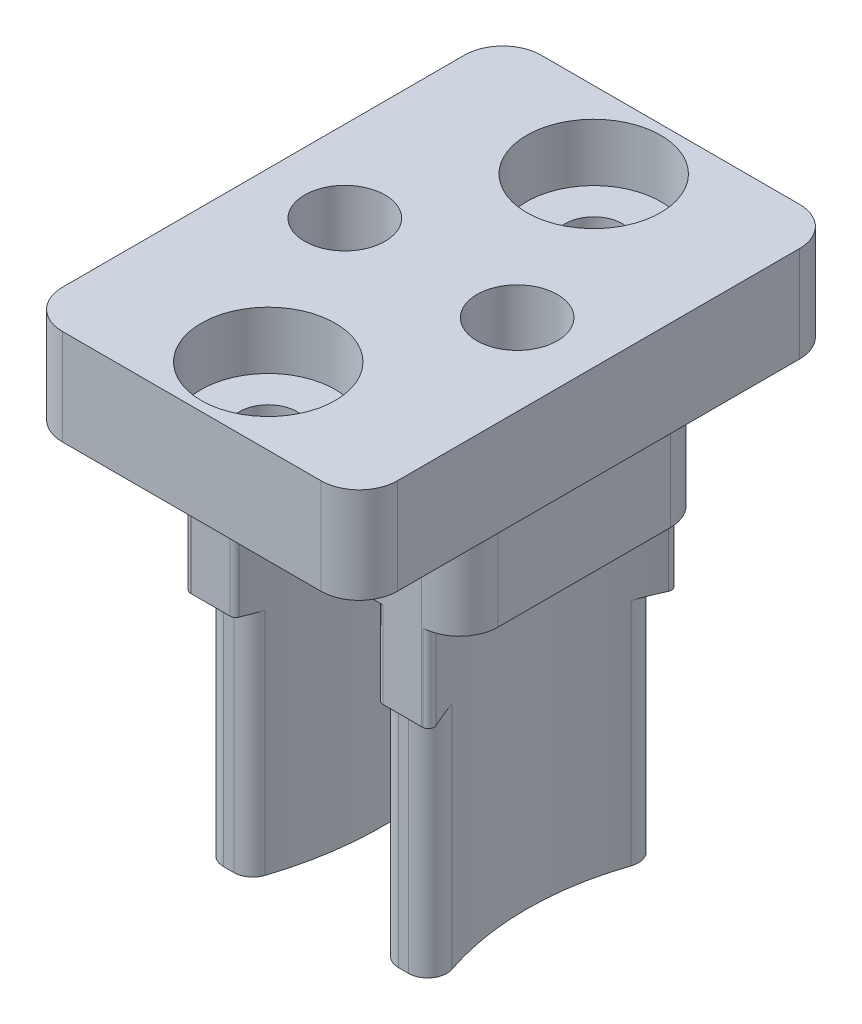
SolidWorks part; units mm, degrees
ref_plane "Front Plane" through (0, 0, 0) normal (0, 0, 1) x (1, 0, 0)
ref_plane "Top Plane" through (0, 0, 0) normal (0, 1, 0) x (1, 0, 0)
ref_plane "Right Plane" through (0, 0, 0) normal (1, 0, 0) x (0, 0, -1)
sketch "Sketch1" plane through (0, 0, 0) normal (0, 1, 0) x (1, 0, 0)
  line L1 (0, 0) -> (123.5, 0)
  line L2 (0, 0) -> (0, -81.5)
  line L3 (0, -81.5) -> (123.5, -81.5)
  line L4 (123.5, 0) -> (123.5, -81.5)
  dimension "D1" = 123.5
  dimension "D2" = 81.5
extrude "Boss-Extrude1" add sketch "Sketch1" along normal blind 8
chamfer "Chamfer1" distance 10 angle 45 2 edges at (123.5, 4, 81.5) (123.5, 4, 0)
sketch "Sketch2" plane through (0, 0, 0) normal (0, -1, 0) x (1, 0, 0)
  line L0 (0, 0) -> (0, 81.5) construction
  line L1 (-3.25, -3.25) -> (126.75, -3.25)
  line L2 (-3.25, -3.25) -> (-3.25, 84.75)
  line L3 (-3.25, 84.75) -> (126.75, 84.75)
  line L4 (126.75, -3.25) -> (126.75, 84.75)
  line L5 (113.5, 0) -> (0, 0) construction
  dimension "D1" = 88
  dimension "D2" = 130
  dimension "D3" = 3.25
  dimension "D4" = 3.25
extrude "Boss-Extrude2" add sketch "Sketch2" along normal blind 9
fillet "Fillet1" radius 2 10 edges at (113.5, 4, 0) (123.5, 4, 10) (123.5, 4, 71.5) (113.5, 4, 81.5) (126.75, -4.5, 84.75) (126.75, -4.5, -3.25) (-3.25, -4.5, -3.25) (0, 4, 0) (-3.25, -4.5, 84.75) (0, 4, 81.5)
sketch "Sketch3" plane through (0, -9, 0) normal (0, -1, 0) x (1, 0, 0)
  line L0 (-3.25, 82.75) -> (-3.25, -1.25) construction
  line L1 (-0.25, 81.75) -> (123.75, 81.75)
  line L2 (-0.25, 81.75) -> (-0.25, -0.25)
  line L3 (-0.25, -0.25) -> (123.75, -0.25)
  line L4 (123.75, 81.75) -> (123.75, -0.25)
  line L5 (-1.25, -3.25) -> (124.75, -3.25) construction
  dimension "D1" = 82
  dimension "D2" = 124
  dimension "D3" = 3
  dimension "D4" = 3
extrude "Cut-Extrude1" cut sketch "Sketch3" against normal blind 2
fillet "Fillet2" radius 2 4 edges at (123.75, -8, 81.75) (123.75, -8, -0.25) (-0.25, -8, -0.25) (-0.25, -8, 81.75)
sketch "Sketch4" plane through (0, 8, 0) normal (0, 1, 0) x (1, 0, 0)
  line L0 (-3.25, -82.75) -> (-3.25, 1.25) construction
  line L1 (112.6716, 0) -> (2, 0) construction
  line L2 (126.75, -40.75) -> (-3.25, -40.75) construction
  line L3 (126.75, 1.25) -> (126.75, -82.75) construction
  circle A0 centre (22.5, -20.85) radius 10
  circle A1 centre (61.5, -20.85) radius 10
  circle A2 centre (100.5, -20.85) radius 10
  circle A3 centre (100.5, -60.65) radius 10
  circle A4 centre (61.5, -60.65) radius 10
  circle A5 centre (22.5, -60.65) radius 10
  dimension "D1" = 25.75
  dimension "D2" = 39
  dimension "D3" = 39
  dimension "D4" = 20.85
  dimension "D5" = 20
extrude "Cut-Extrude2" cut sketch "Sketch4" against normal through all
sketch "Sketch5" plane through (0, -7, 0) normal (0, -1, 0) x (1, 0, 0)
  line L0 (126.75, 40.75) -> (-3.25, 40.75) construction
  line L1 (126.75, -1.25) -> (126.75, 82.75) construction
  line L2 (-3.25, 82.75) -> (-3.25, -1.25) construction
  circle A0 centre (22.5, 60.65) radius 14.5
  circle A1 centre (22.5, 60.65) radius 17
  circle A2 centre (61.5, 60.65) radius 14.5
  circle A3 centre (61.5, 60.65) radius 17
  circle A4 centre (100.5, 60.65) radius 14.5
  circle A5 centre (100.5, 60.65) radius 17
  circle A6 centre (100.5, 20.85) radius 17
  circle A7 centre (100.5, 20.85) radius 14.5
  circle A8 centre (61.5, 20.85) radius 17
  circle A9 centre (61.5, 20.85) radius 14.5
  circle A10 centre (22.5, 20.85) radius 17
  circle A11 centre (22.5, 20.85) radius 14.5
  dimension "D1" = 29
  dimension "D2" = 34
extrude "Boss-Extrude3" add sketch "Sketch5" along normal blind 16.5
sketch "Sketch6" plane through (0, -23.5, 0) normal (0, -1, 0) x (1, 0, 0)
  line L0 (100.5, 20.85) -> (142.0051, 20.85) construction
  line L1 (4.5, 26.85) -> (118.5, 26.85)
  line L2 (4.5, 26.85) -> (4.5, 14.85)
  line L3 (4.5, 14.85) -> (118.5, 14.85)
  line L4 (118.5, 26.85) -> (118.5, 14.85)
  line L5 (126.75, 40.75) -> (-3.25, 40.75) construction
  line L6 (-23.5, 39.1) -> (146.5, 39.1)
  line L7 (-23.5, 39.1) -> (-23.5, 2.6)
  line L8 (-23.5, 2.6) -> (146.5, 2.6)
  line L9 (146.5, 39.1) -> (146.5, 2.6)
  line L10 (-23.5, 39.1) -> (146.5, 2.6) construction
  line L11 (-23.5, 2.6) -> (146.5, 39.1) construction
  line L12 (126.75, -1.25) -> (126.75, 82.75) construction
  line L13 (-3.25, 82.75) -> (-3.25, -1.25) construction
  line L14 (-23.5, 78.9) -> (146.5, 42.4) construction
  line L15 (-23.5, 42.4) -> (146.5, 78.9) construction
  line L16 (100.5, 60.65) -> (142.0051, 60.65) construction
  line L17 (146.5, 42.4) -> (146.5, 78.9)
  line L18 (-23.5, 78.9) -> (146.5, 78.9)
  line L19 (-23.5, 42.4) -> (-23.5, 78.9)
  line L20 (-23.5, 42.4) -> (146.5, 42.4)
  line L21 (118.5, 54.65) -> (118.5, 66.65)
  line L22 (4.5, 66.65) -> (118.5, 66.65)
  line L23 (4.5, 54.65) -> (4.5, 66.65)
  line L24 (4.5, 54.65) -> (118.5, 54.65)
  circle A0 centre (22.5, 20.85) radius 10 construction
  point P11 (61.5, 20.85)
  point P31 (61.5, 60.65)
  dimension "D1" = 6
  dimension "D2" = 12
  dimension "D3" = 18
  dimension "D4" = 18
  dimension "D5" = 36.5
  dimension "D6" = 170
extrude "Cut-Extrude3" cut sketch "Sketch6" against normal blind 12
fillet "Fillet3" radius 1 48 edges at (6.594, -17.5, 66.65) (38.406, -17.5, 66.65) (35.7004, -17.5, 66.65) (9.2996, -17.5, 66.65) (9.2996, -17.5, 54.65) (35.7004, -17.5, 54.65) (6.594, -17.5, 54.65) (38.406, -17.5, 54.65) (74.7004, -17.5, 66.65) (48.2996, -17.5, 66.65) (45.594, -17.5, 66.65) (77.406, -17.5, 66.65) (48.2996, -17.5, 54.65) (74.7004, -17.5, 54.65) (45.594, -17.5, 54.65) (77.406, -17.5, 54.65) (113.7004, -17.5, 66.65) (87.2996, -17.5, 66.65) (84.594, -17.5, 66.65) (116.406, -17.5, 66.65) (87.2996, -17.5, 54.65) (113.7004, -17.5, 54.65) (84.594, -17.5, 54.65) (116.406, -17.5, 54.65) (113.7004, -17.5, 26.85) (87.2996, -17.5, 26.85) (116.406, -17.5, 26.85) (84.594, -17.5, 26.85) (116.406, -17.5, 14.85) (84.594, -17.5, 14.85) (87.2996, -17.5, 14.85) (113.7004, -17.5, 14.85) (48.2996, -17.5, 14.85) (74.7004, -17.5, 14.85) (77.406, -17.5, 14.85) (45.594, -17.5, 14.85) (77.406, -17.5, 26.85) (45.594, -17.5, 26.85) (74.7004, -17.5, 26.85) (48.2996, -17.5, 26.85) (38.406, -17.5, 26.85) (6.594, -17.5, 26.85) (35.7004, -17.5, 26.85) (9.2996, -17.5, 26.85) (38.406, -17.5, 14.85) (6.594, -17.5, 14.85) (9.2996, -17.5, 14.85) (35.7004, -17.5, 14.85)
sketch "Sketch7" plane through (0, -23.5, 0) normal (0, -1, 0) x (1, 0, 0)
  line L0 (22.5, 20.85) -> (9.8511, 20.85) construction
  line L1 (22.5, 20.85) -> (22.5, 13.7381) construction
  line L2 (22.5, 20.85) -> (61.5, 20.85) construction
  line L3 (42, 20.85) -> (42, 5.6594) construction
  line L4 (100.5, 20.85) -> (61.5, 20.85) construction
  line L5 (81, 20.85) -> (81, 5.6594) construction
  line L6 (126.75, 40.75) -> (-3.25, 40.75) construction
  line L7 (126.75, -1.25) -> (126.75, 82.75) construction
  line L8 (-3.25, 82.75) -> (-3.25, -1.25) construction
  circle A0 centre (6.75, 20.85) radius 0.85
  circle A1 centre (38.25, 20.85) radius 0.85
  circle A2 centre (45.75, 20.85) radius 0.85
  circle A3 centre (77.25, 20.85) radius 0.85
  circle A4 centre (84.75, 20.85) radius 0.85
  circle A5 centre (116.25, 20.85) radius 0.85
  circle A6 centre (116.25, 60.65) radius 0.85
  circle A7 centre (84.75, 60.65) radius 0.85
  circle A8 centre (77.25, 60.65) radius 0.85
  circle A9 centre (45.75, 60.65) radius 0.85
  circle A10 centre (38.25, 60.65) radius 0.85
  circle A11 centre (6.75, 60.65) radius 0.85
  dimension "D1" = 1.7
  dimension "D2" = 15.75
extrude "Cut-Extrude4" cut sketch "Sketch7" against normal blind 20.75
sketch "Sketch11" plane through (0, 0, 0) normal (0, 0, -1) x (-1, 0, 0)
  line L1 (-126.75, 10) -> (3.25, 10)
  line L2 (-126.75, 10) -> (-126.75, 0)
  line L3 (-126.75, 0) -> (3.25, 0)
  line L4 (3.25, 10) -> (3.25, 0)
  dimension "D1" = 10
extrude "Cut-Extrude8" cut sketch "Sketch11" against normal through all
sketch "Sketch13" plane through (0, 0, 0) normal (0, 1, 0) x (1, 0, 0)
  line L0 (77.25, -20.85) -> (80.5958, -20.85) construction
  line L1 (77.25, -60.65) -> (63.0285, -60.65) construction
  circle A0 centre (116.25, -60.65) radius 2.1
  circle A1 centre (85.5, -60.65) radius 2.1
  circle A2 centre (76.5, -60.65) radius 2.1
  circle A3 centre (116.25, -20.85) radius 2.1
  circle A4 centre (85.5, -20.85) radius 2.1
  circle A5 centre (76.5, -20.85) radius 2.1
  circle A6 centre (46.5, -20.85) radius 2.1
  circle A7 centre (37.5, -20.85) radius 2.1
  circle A8 centre (6.75, -20.85) radius 2.1
  circle A9 centre (6.75, -60.65) radius 2.1
  circle A10 centre (37.5, -60.65) radius 2.1
  circle A11 centre (46.5, -60.65) radius 2.1
  circle A12 centre (84.75, -60.65) radius 0.85 construction
  circle A13 centre (77.25, -60.65) radius 0.85 construction
  circle A14 centre (45.75, -60.65) radius 0.85 construction
  circle A15 centre (38.25, -60.65) radius 0.85 construction
  circle A16 centre (45.75, -20.85) radius 0.85 construction
  circle A17 centre (38.25, -20.85) radius 0.85 construction
  circle A18 centre (77.25, -20.85) radius 0.85 construction
  circle A19 centre (84.75, -20.85) radius 0.85 construction
  dimension "D1" = 4.2
  dimension "D3" = 0.75
  dimension "D2" = 0.75
  dimension "D4" = 0.75
  dimension "D5" = 0.75
  dimension "D6" = 0.75
  dimension "D7" = 0.75
  dimension "D8" = 0.75
  dimension "D9" = 0.75
extrude "Cut-Extrude9" cut sketch "Sketch13" against normal blind 6
sketch "Sketch15" plane through (0, 0, 0) normal (0, 1, 0) x (1, 0, 0)
  line L4 (126.75, -82.75) -> (126.75, 1.25)
  line L5 (124.75, 3.25) -> (-1.25, 3.25)
  line L6 (-3.25, 1.25) -> (-3.25, -82.75)
  line L7 (-1.25, -84.75) -> (124.75, -84.75)
  line L8 (126.75, -82.75) -> (126.75, 1.25)
  line L9 (124.75, 3.25) -> (-1.25, 3.25)
  line L10 (-3.25, 1.25) -> (-3.25, -82.75)
  line L11 (-1.25, -84.75) -> (124.75, -84.75)
  circle A0 centre (6.75, -60.65) radius 2.1 construction
  circle A1 centre (22.5, -60.65) radius 10 construction
  circle A2 centre (37.5, -60.65) radius 2.1 construction
  circle A3 centre (46.5, -60.65) radius 2.1 construction
  arc A4 (124.75, -84.75) -> (126.75, -82.75) centre (124.75, -82.75) ccw
  arc A5 (126.75, 1.25) -> (124.75, 3.25) centre (124.75, 1.25) ccw
  arc A6 (-1.25, 3.25) -> (-3.25, 1.25) centre (-1.25, 1.25) ccw
  arc A7 (-3.25, -82.75) -> (-1.25, -84.75) centre (-1.25, -82.75) ccw
  arc A8 (124.75, -84.75) -> (126.75, -82.75) centre (124.75, -82.75) ccw
  arc A9 (126.75, 1.25) -> (124.75, 3.25) centre (124.75, 1.25) ccw
  arc A10 (-1.25, 3.25) -> (-3.25, 1.25) centre (-1.25, 1.25) ccw
  arc A11 (-3.25, -82.75) -> (-1.25, -84.75) centre (-1.25, -82.75) ccw
  circle A12 centre (61.5, -60.65) radius 10 construction
  circle A13 centre (76.5, -60.65) radius 2.1 construction
  circle A14 centre (100.5, -60.65) radius 10 construction
  circle A15 centre (116.25, -60.65) radius 2.1 construction
  circle A16 centre (116.25, -20.85) radius 2.1 construction
  circle A17 centre (100.5, -20.85) radius 10 construction
  circle A18 centre (85.5, -20.85) radius 2.1 construction
  circle A19 centre (76.5, -20.85) radius 2.1 construction
  circle A20 centre (61.5, -20.85) radius 10 construction
  circle A21 centre (46.5, -20.85) radius 2.1 construction
  circle A22 centre (37.5, -20.85) radius 2.1 construction
  circle A23 centre (22.5, -20.85) radius 10 construction
  circle A24 centre (6.75, -60.65) radius 2.1
  circle A25 centre (22.5, -60.65) radius 10
  circle A26 centre (37.5, -60.65) radius 2.1
  circle A27 centre (46.5, -60.65) radius 2.1
  circle A28 centre (61.5, -60.65) radius 10
  circle A29 centre (76.5, -60.65) radius 2.1
  circle A30 centre (100.5, -60.65) radius 10
  circle A31 centre (116.25, -60.65) radius 2.1
  circle A32 centre (116.25, -20.85) radius 2.1
  circle A33 centre (100.5, -20.85) radius 10
  circle A34 centre (85.5, -20.85) radius 2.1
  circle A35 centre (76.5, -20.85) radius 2.1
  circle A36 centre (61.5, -20.85) radius 10
  circle A37 centre (46.5, -20.85) radius 2.1
  circle A38 centre (37.5, -20.85) radius 2.1
  circle A39 centre (22.5, -20.85) radius 10
  circle A40 centre (85.5, -60.65) radius 2.1 construction
  circle A41 centre (85.5, -60.65) radius 2.1
  circle A42 centre (6.75, -20.85) radius 2.1 construction
  circle A43 centre (6.75, -20.85) radius 2.1
  dimension "D1" = 0
extrude "Boss-Extrude4" add sketch "Sketch15" along normal blind 3
sketch "Sketch16" plane through (0, 3, 0) normal (0, 1, 0) x (1, 0, 0)
  line L0 (77.25, -60.65) -> (84.75, -60.65) construction
  line L2 (72.25, -48.15) -> (89.75, -48.15)
  line L3 (72.25, -48.15) -> (72.25, -73.15)
  line L4 (72.25, -73.15) -> (89.75, -73.15)
  line L5 (89.75, -48.15) -> (89.75, -73.15)
  line L6 (72.25, -48.15) -> (89.75, -73.15) construction
  line L7 (72.25, -73.15) -> (89.75, -48.15) construction
  line L8 (-21.6591, 13.8545) -> (145.6938, 13.8545)
  line L9 (-21.6591, 13.8545) -> (-21.6591, -97.3769)
  line L10 (-21.6591, -97.3769) -> (145.6938, -97.3769)
  line L11 (145.6938, 13.8545) -> (145.6938, -97.3769)
  point P4 (81, -60.65)
  dimension "D1" = 17.5
  dimension "D2" = 25
extrude "Cut-Extrude10" cut sketch "Sketch16" against normal through all
sketch "Sketch17" plane through (0, 3, 0) normal (0, 1, 0) x (1, 0, 0)
  line L0 (77.25, -60.65) -> (84.75, -60.65) construction
  line L2 (73, -67.15) -> (89, -67.15)
  line L3 (73, -67.15) -> (73, -54.15)
  line L4 (73, -54.15) -> (89, -54.15)
  line L5 (89, -67.15) -> (89, -54.15)
  line L6 (73, -67.15) -> (89, -54.15) construction
  line L7 (73, -54.15) -> (89, -67.15) construction
  line L8 (72.25, -73.15) -> (89.75, -73.15)
  line L9 (72.25, -73.15) -> (72.25, -48.15)
  line L10 (72.25, -48.15) -> (89.75, -48.15)
  line L11 (89.75, -73.15) -> (89.75, -48.15)
  point P4 (81, -60.65)
  dimension "D1" = 13
  dimension "D2" = 16
extrude "Cut-Extrude11" cut sketch "Sketch17" against normal through all from offset 5 offset against normal yes
fillet "Fillet4" radius 2 8 edges at (72.25, 0.5, 73.15) (89.75, 0.5, 73.15) (73, -4.5, 54.15) (89, -4.5, 54.15) (72.25, 0.5, 48.15) (89.75, 0.5, 48.15) (73, -4.5, 67.15) (89, -4.5, 67.15)
sketch "Sketch18" plane through (0, 3, 0) normal (0, 1, 0) x (1, 0, 0)
  line L0 (87.75, -48.15) -> (74.25, -48.15) construction
  line L1 (77.25, -60.65) -> (84.75, -60.65) construction
  circle A0 centre (81, -52.15) radius 1.5
  circle A1 centre (81, -52.15) radius 3.5 construction
  circle A2 centre (81, -69.15) radius 1.5
  point P5 (81, -48.15)
  dimension "D1" = 3
  dimension "D2" = 7
  dimension "D3" = 4
extrude "Cut-Extrude12" cut sketch "Sketch18" against normal blind 10
sketch "Sketch19" plane through (0, 3, 0) normal (0, 1, 0) x (1, 0, 0)
  circle A0 centre (81, -52.15) radius 3.5
  circle A1 centre (81, -69.15) radius 3.5
  dimension "D1" = 7
extrude "Cut-Extrude13" cut sketch "Sketch19" against normal blind 3
fillet "Fillet5" radius 0.3 8 edges at (87.5061, -9.25, 67.0849) (84.7917, -9.25, 67.15) (77.2083, -9.25, 67.15) (74.4939, -9.25, 67.0849) (87.5061, -9.25, 54.2151) (84.7917, -9.25, 54.15) (77.2083, -9.25, 54.15) (74.4939, -9.25, 54.2151)
